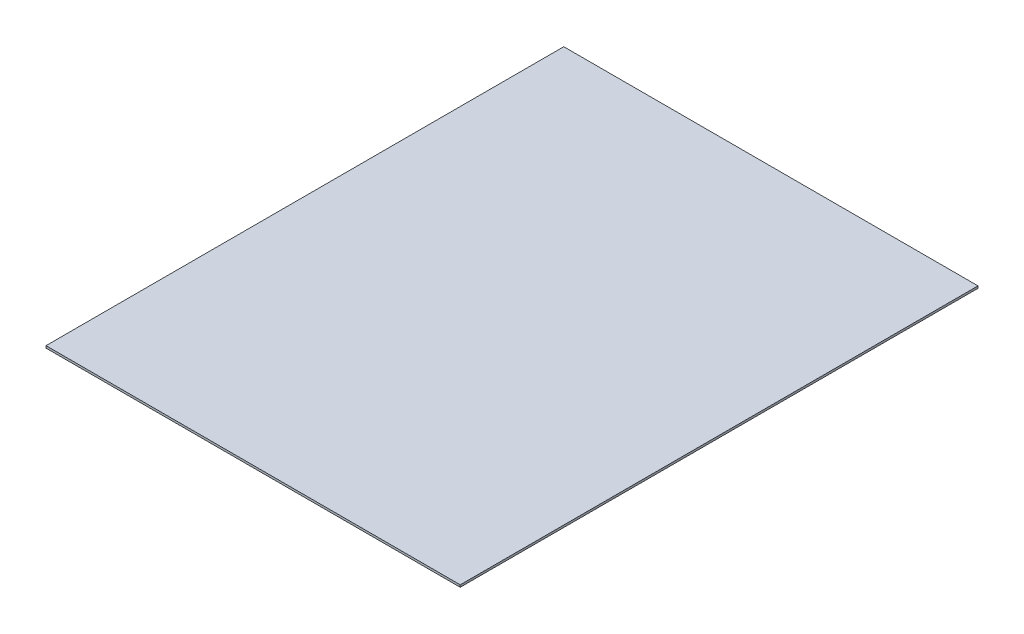
SolidWorks part; units mm, degrees
ref_plane "Front Plane" through (0, 0, 0) normal (0, 0, 1) x (1, 0, 0)
ref_plane "Top Plane" through (0, 0, 0) normal (0, 1, 0) x (1, 0, 0)
ref_plane "Right Plane" through (0, 0, 0) normal (1, 0, 0) x (0, 0, -1)
sketch "Sketch1" plane through (0, 0, 0) normal (0, 1, 0) x (1, 0, 0)
  line L1 (-609.6, -762) -> (609.6, -762)
  line L2 (-609.6, -762) -> (-609.6, 762)
  line L3 (-609.6, 762) -> (609.6, 762)
  line L4 (609.6, -762) -> (609.6, 762)
  line L5 (-609.6, -762) -> (609.6, 762) construction
  line L6 (-609.6, 762) -> (609.6, -762) construction
  point P0 (0, 0)
  dimension "D1" = 1219.2
  dimension "D2" = 1524
extrude "Boss-Extrude1" add sketch "Sketch1" along normal blind 6.35
